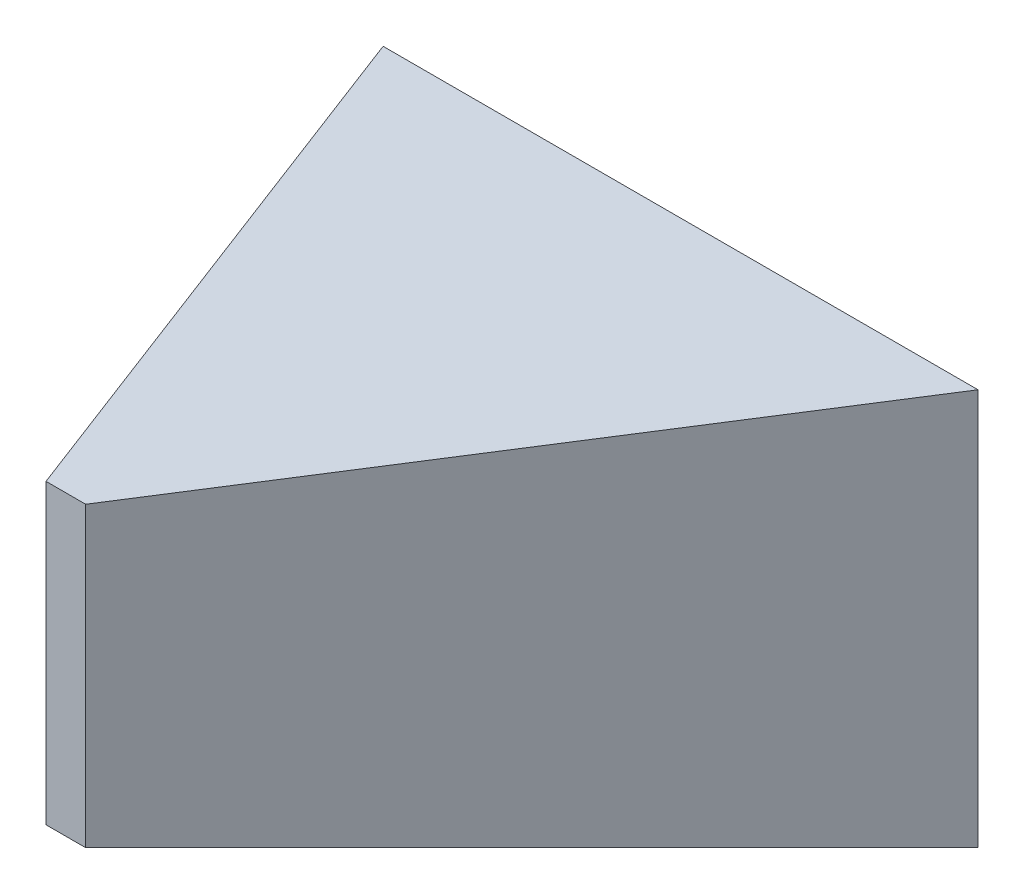
SolidWorks part; units mm, degrees
ref_plane "Front" through (0, 0, 0) normal (0, 0, 1) x (1, 0, 0)
ref_plane "Top" through (0, 0, 0) normal (0, 1, 0) x (1, 0, 0)
ref_plane "Right" through (0, 0, 0) normal (1, 0, 0) x (0, 0, -1)
sketch "Sketch1" plane through (0, 0, 0) normal (0, 0, 1) x (1, 0, 0)
  line L0 (0, 0) -> (30, 0)
  line L1 (0, 0) -> (0, 20)
  line L2 (30, 0) -> (30, 20)
  line L3 (0, 20) -> (30, 20)
  dimension "D1" = 20
  dimension "D2" = 30
ref_plane "Plane1" through (0, 0, 25) normal (0, 0, 1) x (1, 0, 0)
sketch "Sketch2" plane through (0, 0, 25) normal (0, 0, 1) x (1, 0, 0)
  line L0 (8, 17.5) -> (8, 2.5)
  line L1 (0, 0) -> (30, 0) construction
  line L2 (0, 0) -> (0, 20) construction
  line L3 (8, 17.5) -> (10, 17.5)
  line L4 (8, 17.5) -> (8, 2.5)
  line L5 (8, 2.5) -> (10, 2.5)
  line L6 (10, 17.5) -> (10, 2.5)
  dimension "D1" = 15
  dimension "D2" = 2.5
  dimension "D3" = 2
  dimension "D4" = 8
loft "Loft2" add profiles "Sketch1" section "Sketch2" section "Sketch1"
